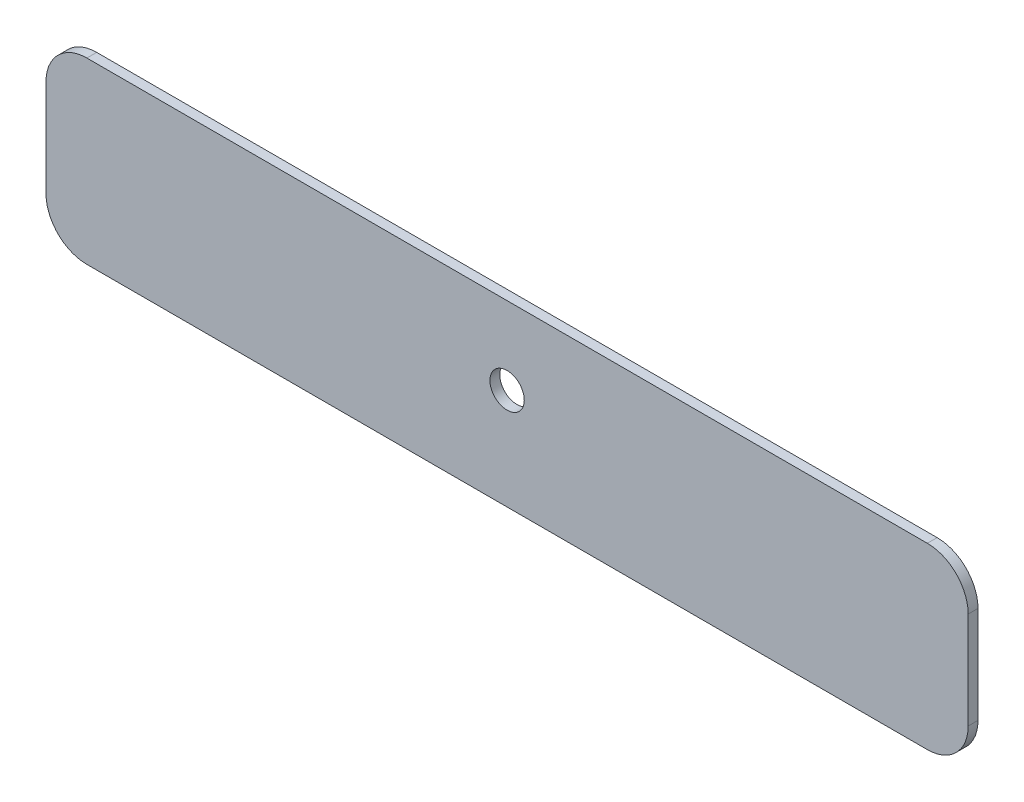
SolidWorks part; units mm, degrees
ref_plane "Front Plane" through (0, 0, 0) normal (0, 0, 1) x (1, 0, 0)
ref_plane "Top Plane" through (0, 0, 0) normal (0, 1, 0) x (1, 0, 0)
ref_plane "Right Plane" through (0, 0, 0) normal (1, 0, 0) x (0, 0, -1)
sketch "Sketch1" plane through (0, 0, 0) normal (0, 0, 1) x (1, 0, 0)
  line L2 (-56.4, 136.5) -> (-56.4, 114.6383)
  line L3 (-56.4, 114.6383) -> (56.4, 114.6383)
  line L4 (56.4, 136.5) -> (56.4, 114.6383)
  line L7 (0, 136.5) -> (-56.4, 136.5)
  line L8 (0, 136.5) -> (56.4, 136.5)
  line L11 (-56.4, 28.6363) -> (-56.4, 107.5) construction
  line L13 (56.4, 131.5) -> (56.4, 111.5) construction
  circle A0 centre (0, 127) radius 2.1 construction
  circle A1 centre (0, 127) radius 2.1
  dimension "D1" = 21.8617
  dimension "D2" = 112.8
  dimension "D3" = 4
extrude "Boss-Extrude1" add sketch "Sketch1" along normal blind 1.2
fillet "Fillet1" radius 5 4 edges at (56.4, 114.6383, 0.6) (-56.4, 114.6383, 0.6) (56.4, 136.5, 0.6) (-56.4, 136.5, 0.6)
